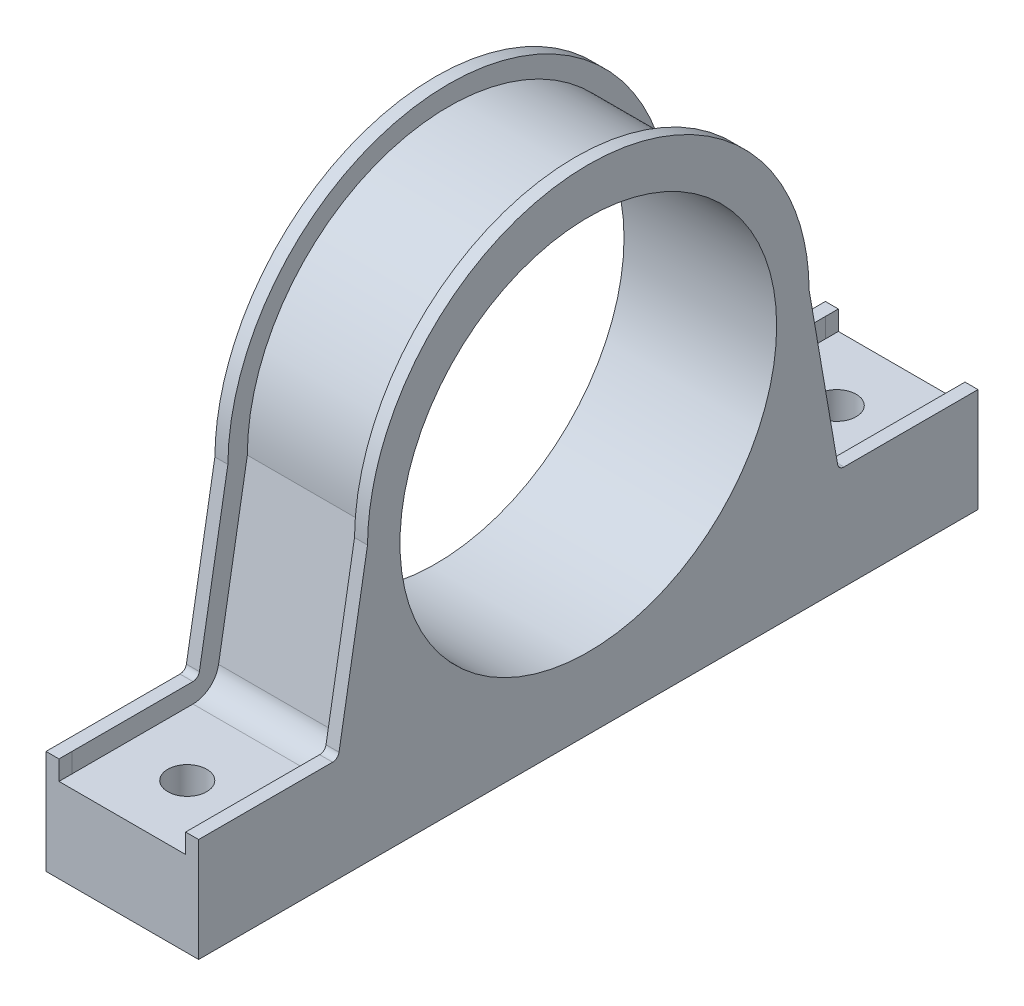
SolidWorks part; units mm, degrees
material "POLIURETAN (11671)"
ref_plane "Płaszczyzna XY" through (0, 0, 0) normal (0, 0, 1) x (1, 0, 0)
ref_plane "Płaszczyzna XZ" through (0, 0, 0) normal (0, 1, 0) x (1, 0, 0)
ref_plane "Płaszczyzna YZ" through (0, 0, 0) normal (1, 0, 0) x (0, 0, -1)
sketch "Szkic2" plane through (0, 0, 0) normal (1, 0, 0) x (0, 0, -1)
  line L0 (60, 6.5) -> (36, 6.5)
  line L1 (-60, -6.5) -> (60, -6.5)
  line L2 (-60, -6.5) -> (-60, 6.5)
  line L3 (-60, 6.5) -> (-36, 6.5)
  line L4 (60, -6.5) -> (60, 6.5)
  line L7 (31, 35.5) -> (36, 6.5)
  line L8 (-60, 6.5) -> (-36, 6.5)
  line L9 (-31, 35.5) -> (-36, 6.5)
  line L12 (36, 6.5) -> (60, 6.5)
  circle A1 centre (0, 33.5) radius 29
  arc A2 (31, 35.5) -> (-31, 35.5) centre (0, 35.5) ccw
  point P0 (0, 0)
  point P11 (0, -6.5)
  dimension "D4" = 40
  dimension "D1" = 120
  dimension "D2" = 13
  dimension "D6" = 24
  dimension "D7" = 24
extrude "Dodanie-wyciągnięcie2" add sketch "Szkic2" along normal blind 23.5
sketch "Szkic3" plane through (0, 6.5, 0) normal (0, 1, 0) x (1, 0, 0)
  line L1 (23.5, 60) -> (0, 60) construction
  line L2 (23.5, -60) -> (0, -60) construction
  circle A0 centre (11.75, 50) radius 3
  circle A1 centre (11.75, -50) radius 3
  point P5 (11.75, 60)
  point P10 (11.75, -60)
  dimension "D1" = 10
  dimension "D2" = 6
  dimension "D3" = 10
extrude "Wytnij-wyciągnięcie1" cut sketch "Szkic3" against normal blind 23.5
fillet "Zaokrąglenie1" radius 4 2 edges at (11.75, 6.5, 36) (11.75, 6.5, -36)
ref_plane "Płaszczyzna1" through (0, 73.5, 0) normal (0, -1, 0) x (-1, 0, 0)
sketch "Szkic4" plane through (0, 73.5, 0) normal (0, -1, 0) x (-1, 0, 0)
  line L0 (0, 60) -> (0, 39.3694) construction
  line L1 (-23.5, 39.3694) -> (-23.5, 60) construction
  line L2 (-23.5, 60) -> (0, 60) construction
  line L3 (-23.5, 31) -> (-23.5, 35.4275) construction
  line L4 (0, 35.4275) -> (0, 31) construction
  line L5 (-23.5, 39.3694) -> (-23.5, 35.4275) construction
  line L6 (0, 35.4275) -> (0, 39.3694) construction
  line L7 (0, -31) -> (0, -35.4275) construction
  line L8 (-23.5, -35.4275) -> (-23.5, -31) construction
  line L9 (0, -31) -> (0, 31) construction
  line L10 (-23.5, 31) -> (-23.5, -31) construction
  line L11 (-23.5, -35.4275) -> (-23.5, -39.3694) construction
  line L12 (0, -39.3694) -> (0, -35.4275) construction
  line L13 (-23.5, -60) -> (-23.5, -39.3694) construction
  line L14 (0, -39.3694) -> (0, -60) construction
  line L15 (0, -60) -> (-23.5, -60) construction
  line L16 (0, 60) -> (0, 39.3694)
  line L17 (-23.5, 39.3694) -> (-23.5, 60)
  line L18 (-2, 60) -> (0, 60)
  line L19 (-23.5, 31) -> (-23.5, 35.4275)
  line L20 (0, 35.4275) -> (0, 31)
  line L21 (-23.5, 39.3694) -> (-23.5, 35.4275)
  line L22 (0, 35.4275) -> (0, 39.3694)
  line L23 (0, -31) -> (0, -35.4275)
  line L24 (-23.5, -35.4275) -> (-23.5, -31)
  line L25 (0, -31) -> (0, 31)
  line L26 (-23.5, 31) -> (-23.5, -31)
  line L27 (-23.5, -35.4275) -> (-23.5, -39.3694)
  line L28 (0, -39.3694) -> (0, -35.4275)
  line L29 (-23.5, -60) -> (-23.5, -39.3694)
  line L30 (0, -39.3694) -> (0, -60)
  line L31 (0, -60) -> (-2, -60)
  line L32 (-2, 58) -> (-2, 60)
  line L33 (-21.5, -60) -> (-23.5, -60)
  line L34 (-21.5, -58) -> (-21.5, 58)
  line L35 (-21.5, 58) -> (-21.5, 60)
  line L36 (-2, -58) -> (-2, 58)
  line L37 (-21.5, -58) -> (-2, 58) construction
  line L38 (-21.5, 58) -> (-11.75, 0) construction
  line L39 (-2, -58) -> (-2, -60)
  line L40 (-21.5, -58) -> (-21.5, -60)
  line L41 (-21.5, 60) -> (-23.5, 60)
  point P15 (-11.75, 0)
  dimension "D3" = 2
  dimension "D4" = 2
extrude "Dodanie-wyciągnięcie3" add sketch "Szkic4" along normal up to next
sketch "Szkic5" plane through (23.5, 0, 0) normal (1, 0, 0) x (0, 0, -1)
  line L1 (-58, 6.5) -> (-60, 6.5)
  line L2 (35.4275, 9.8204) -> (31, 35.5) construction
  line L3 (35.4275, 9.8204) -> (31, 35.5)
  line L4 (39.3694, 6.5) -> (58, 6.5) construction
  line L5 (39.3694, 6.5) -> (58, 6.5)
  line L6 (-35.4275, 9.8204) -> (-31, 35.5) construction
  line L7 (-35.4275, 9.8204) -> (-31, 35.5)
  line L8 (-39.3694, 6.5) -> (-58, 6.5) construction
  line L9 (-39.3694, 6.5) -> (-58, 6.5)
  line L10 (58, 6.5) -> (60, 6.5)
  line L11 (60, -6.5) -> (60, 73.5) construction
  line L12 (-58, 9.5) -> (-60, 9.5)
  line L13 (-39.3694, 9.5) -> (-58, 9.5)
  line L14 (-38.3839, 10.3301) -> (-33.999, 35.7626)
  line L15 (38.3839, 10.3301) -> (33.999, 35.7626)
  line L16 (39.3694, 9.5) -> (58, 9.5)
  line L17 (58, 9.5) -> (60, 9.5)
  line L18 (-60, 9.5) -> (-60, 73.5)
  line L19 (-12.925, 73.5) -> (12.925, 73.5) construction
  line L20 (-60, -6.5) -> (-60, 73.5) construction
  line L21 (-60, 73.5) -> (60, 73.5)
  line L22 (60, 73.5) -> (60, 9.5)
  arc A0 (31, 35.5) -> (-31, 35.5) centre (0, 35.5) ccw construction
  arc A1 (31, 35.5) -> (-31, 35.5) centre (0, 35.5) ccw
  arc A2 (35.4275, 9.8204) -> (39.3694, 6.5) centre (39.3694, 10.5) ccw construction
  arc A3 (35.4275, 9.8204) -> (39.3694, 6.5) centre (39.3694, 10.5) ccw
  arc A4 (-39.3694, 6.5) -> (-35.4275, 9.8204) centre (-39.3694, 10.5) ccw construction
  arc A5 (-39.3694, 6.5) -> (-35.4275, 9.8204) centre (-39.3694, 10.5) ccw
  arc A6 (-39.3694, 9.5) -> (-38.3839, 10.3301) centre (-39.3694, 10.5) ccw
  arc A7 (33.999, 35.7626) -> (-33.999, 35.7626) centre (0, 35.5) ccw
  arc A8 (38.3839, 10.3301) -> (39.3694, 9.5) centre (39.3694, 10.5) ccw
  line M4 (35.4275, 73.5) -> (35.4275, 9.8204)
  line M5 (35.4275, 73.5) -> (31, 73.5)
  line M6 (31, 73.5) -> (31, 35.5)
  line M7 (31, 73.5) -> (-31, 73.5)
  line M8 (-31, 73.5) -> (-31, 35.5)
  line M9 (-31, 73.5) -> (-35.4275, 73.5)
  line M10 (-35.4275, 73.5) -> (-35.4275, 9.8204)
  line M11 (-35.4275, 73.5) -> (-39.3694, 73.5)
  line M12 (-39.3694, 73.5) -> (-39.3694, 6.5)
  line M13 (-39.3694, 73.5) -> (-60, 73.5)
  line M14 (-60, 73.5) -> (-60, -6.5)
  line M16 (60, -6.5) -> (60, 73.5)
  line M17 (60, 73.5) -> (39.3694, 73.5)
  line M18 (39.3694, 73.5) -> (39.3694, 6.5)
  line M19 (39.3694, 73.5) -> (35.4275, 73.5)
  dimension "D1" = 3
extrude "Wytnij-wyciągnięcie2" cut sketch "Szkic5" against normal blind 23.5 contours L13 L12 M12 M13 M14 | A6 L14 M12 M10 M11 | A7 M6 M7 M8 | A7 L14 M8 M9 M10 | L15 A8 M18 M19 M4 | A7 L15 M4 M5 M6 | L16 L17 M16 M17 M18
